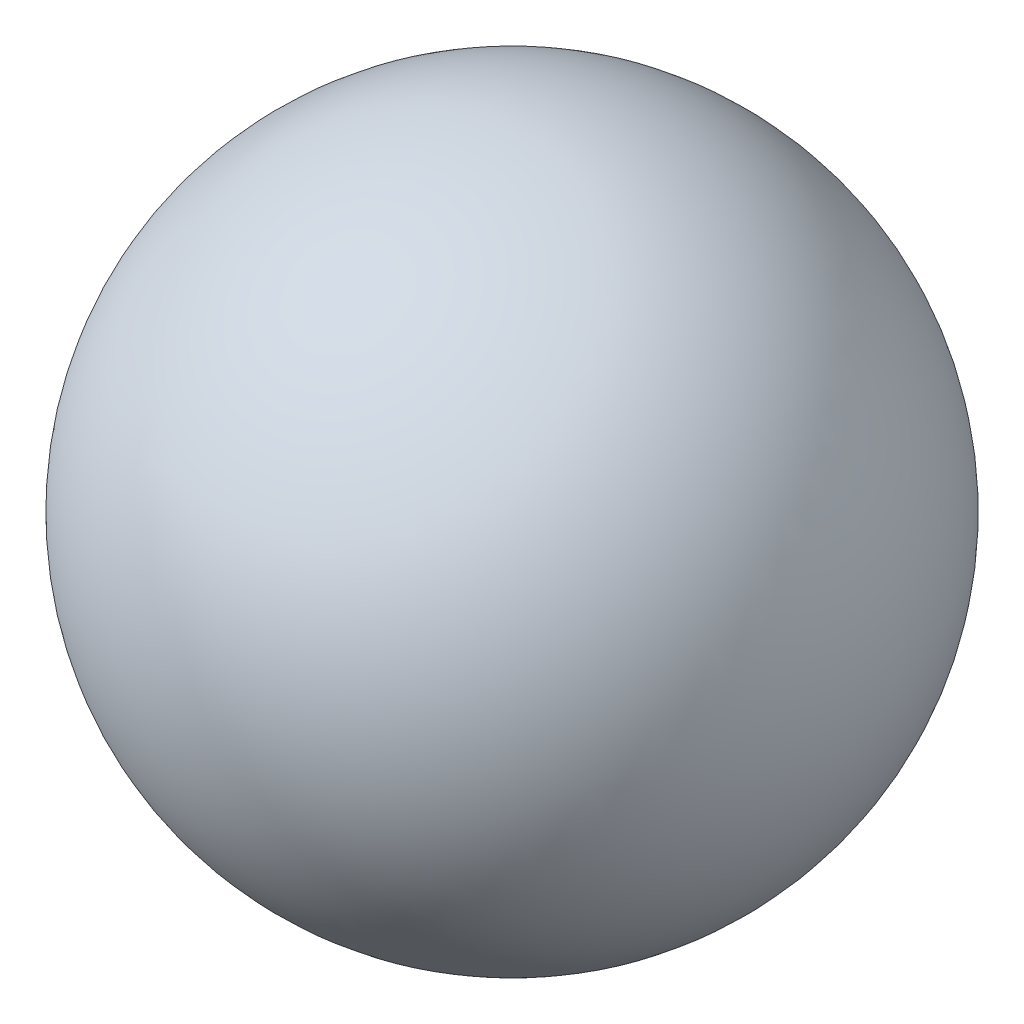
SolidWorks part; units mm, degrees
material "ｼﾘｺﾝ ｺﾞﾑ"
ref_plane "正面" through (0, 0, 0) normal (0, 0, 1) x (1, 0, 0)
ref_plane "平面" through (0, 0, 0) normal (0, 1, 0) x (1, 0, 0)
ref_plane "右側面" through (0, 0, 0) normal (1, 0, 0) x (0, 0, -1)
sketch "ｽｹｯﾁ1" plane through (0, 0, 0) normal (0, 0, 1) x (1, 0, 0)
  line L0 (0, -126.5) -> (0, 126.5) construction
  line L1 (0, 125) -> (0, -125)
  arc A0 (0, 125) -> (0, -125) centre (0, 0) cw
  dimension "D1" = 250
revolve "回転1" add sketch "ｽｹｯﾁ1" angle 360 about L1
